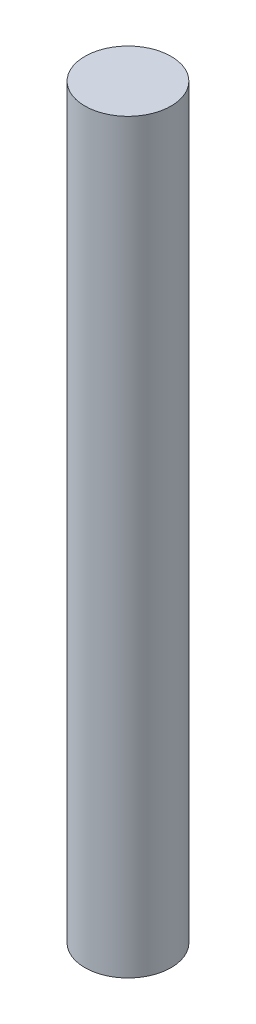
SolidWorks part; units mm, degrees
ref_plane "Front Plane" through (0, 0, 0) normal (0, 0, 1) x (1, 0, 0)
ref_plane "Top Plane" through (0, 0, 0) normal (0, 1, 0) x (1, 0, 0)
ref_plane "Right Plane" through (0, 0, 0) normal (1, 0, 0) x (0, 0, -1)
sketch "Sketch1" plane through (0, 0, 0) normal (0, 1, 0) x (1, 0, 0)
  circle A0 centre (0, 0) radius 1.5875
  dimension "D1" = 3.175
extrude "Boss-Extrude1" add sketch "Sketch1" along normal blind 27.5
